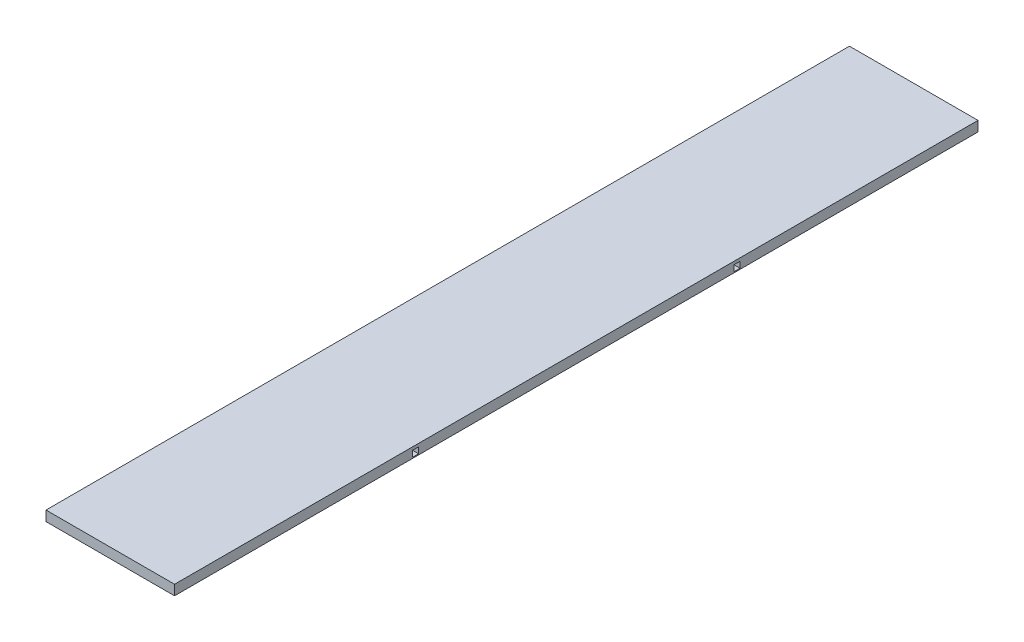
SolidWorks part; units mm, degrees
material "Polyurethane Foam Flexible"
ref_plane "Front Plane" through (0, 0, 0) normal (0, 0, 1) x (1, 0, 0)
ref_plane "Top Plane" through (0, 0, 0) normal (0, 1, 0) x (1, 0, 0)
ref_plane "Right Plane" through (0, 0, 0) normal (1, 0, 0) x (0, 0, -1)
sketch "Sketch1" plane through (0, 0, 0) normal (0, 1, 0) x (1, 0, 0)
  line L1 (-203.2, 1270) -> (203.2, 1270)
  line L2 (-203.2, 1270) -> (-203.2, -1270)
  line L3 (-203.2, -1270) -> (203.2, -1270)
  line L4 (203.2, 1270) -> (203.2, -1270)
  line L5 (-203.2, 1270) -> (203.2, -1270) construction
  line L6 (-203.2, -1270) -> (203.2, 1270) construction
  point P0 (0, 0)
  dimension "D1" = 406.4
  dimension "D2" = 2540
extrude "Boss-Extrude1" add sketch "Sketch1" along normal blind 31.75
sketch "Sketch2" plane through (203.2, 0, 0) normal (1, 0, 0) x (0, 0, -1)
  line L0 (-1270, 0) -> (1270, 0) construction
  line L1 (-517.525, 22.225) -> (-498.475, 22.225)
  line L2 (-517.525, 22.225) -> (-517.525, 3.175)
  line L3 (-517.525, 3.175) -> (-498.475, 3.175)
  line L4 (-498.475, 22.225) -> (-498.475, 3.175)
  line L5 (-517.525, 22.225) -> (-498.475, 3.175) construction
  line L6 (-517.525, 3.175) -> (-498.475, 22.225) construction
  line L7 (-1270, 31.75) -> (-1270, 0) construction
  line L8 (1270, 31.75) -> (1270, 0) construction
  line L9 (498.475, 22.225) -> (517.525, 22.225)
  line L10 (498.475, 22.225) -> (498.475, 3.175)
  line L11 (498.475, 3.175) -> (517.525, 3.175)
  line L12 (517.525, 22.225) -> (517.525, 3.175)
  line L13 (498.475, 22.225) -> (517.525, 3.175) construction
  line L14 (498.475, 3.175) -> (517.525, 22.225) construction
  point P0 (-508, 12.7)
  point P9 (508, 12.7)
  dimension "D1" = 19.05
  dimension "D2" = 19.05
  dimension "D3" = 3.175
  dimension "D4" = 762
  dimension "D5" = 19.05
  dimension "D6" = 19.05
  dimension "D7" = 3.175
  dimension "D8" = 762
extrude "Cut-Extrude1" cut sketch "Sketch2" against normal up to surface (406.4 mm away) up to face at (-203.2, 15.875, 0)
